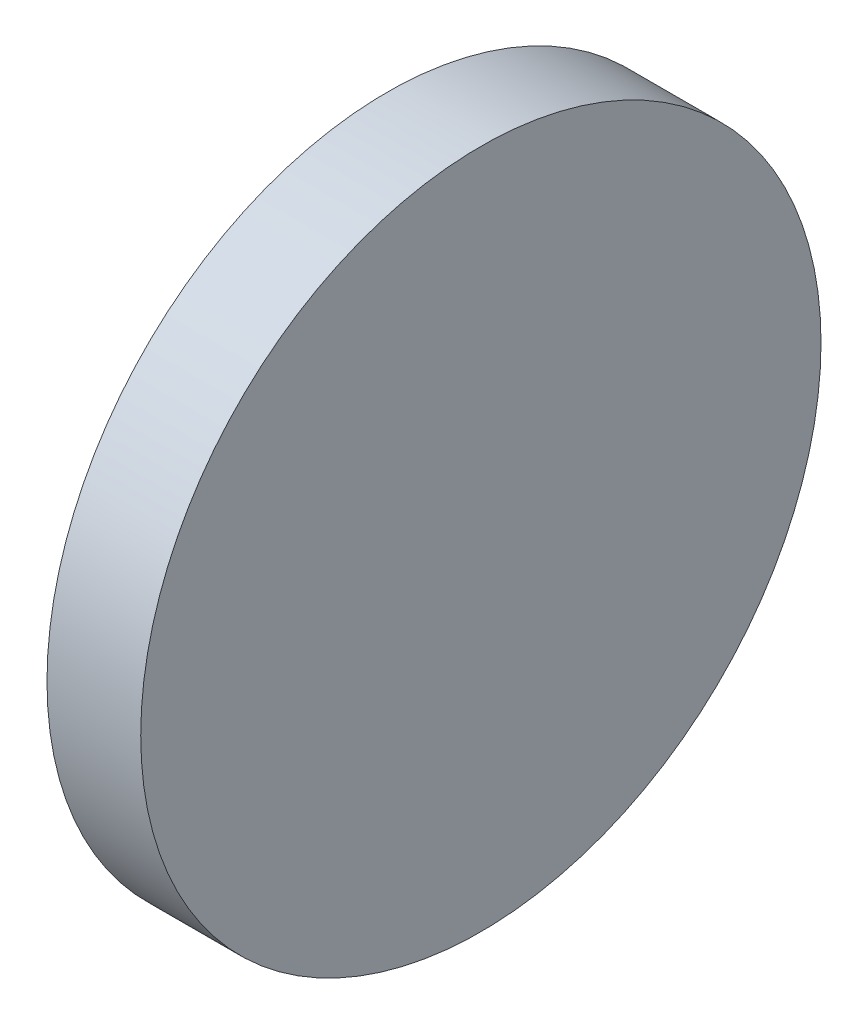
SolidWorks part; units mm, degrees
ref_plane "前视基准面" through (0, 0, 0) normal (0, 0, 1) x (1, 0, 0)
ref_plane "上视基准面" through (0, 0, 0) normal (0, 1, 0) x (1, 0, 0)
ref_plane "右视基准面" through (0, 0, 0) normal (1, 0, 0) x (0, 0, -1)
sketch "草图1" plane through (0, 0, 0) normal (0, 0, 1) x (1, 0, 0)
  line L0 (0, 12.7) -> (0, 0)
  line L2 (0, 12.7) -> (3.5, 12.7)
  line L3 (0, 0) -> (3.5, 0)
  line L4 (3.5, 12.7) -> (3.5, 0)
  dimension "D1" = 12.7
  dimension "D2" = 3.5
revolve "旋转2" add sketch "草图1" angle 360 about L3
